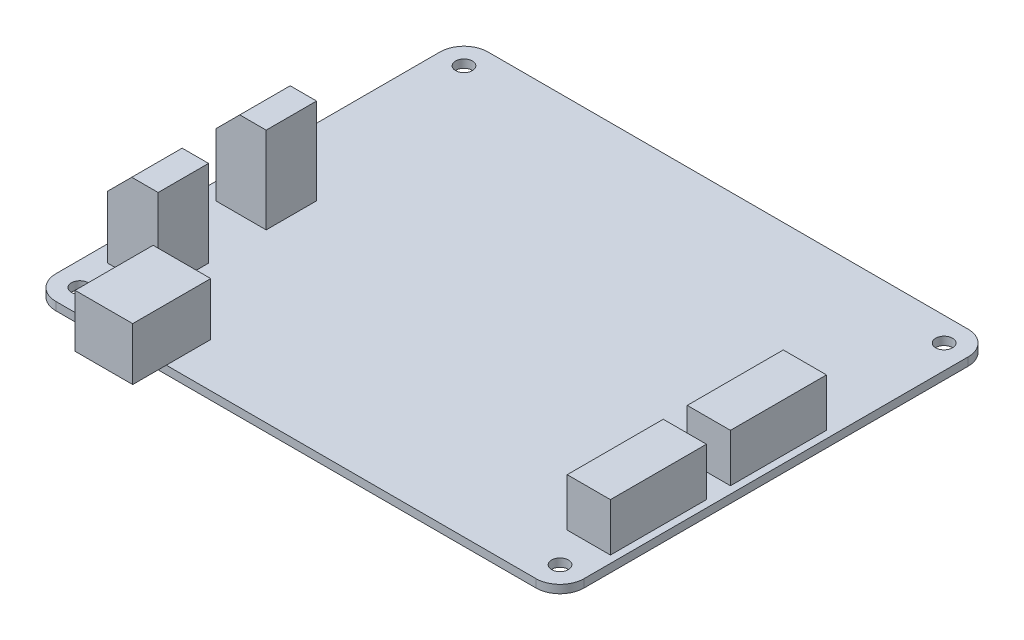
SolidWorks part; units mm, degrees
ref_plane "Front Plane" through (0, 0, 0) normal (0, 0, 1) x (1, 0, 0)
ref_plane "Top Plane" through (0, 0, 0) normal (0, 1, 0) x (1, 0, 0)
ref_plane "Right Plane" through (0, 0, 0) normal (1, 0, 0) x (0, 0, -1)
sketch "Sketch1" plane through (0, 0, 0) normal (0, 1, 0) x (1, 0, 0)
  line L1 (-55, -45) -> (55, -45)
  line L2 (-55, -45) -> (-55, 45)
  line L3 (-55, 45) -> (55, 45)
  line L4 (55, -45) -> (55, 45)
  line L5 (-55, -45) -> (55, 45) construction
  line L6 (-55, 45) -> (55, -45) construction
  point P0 (0, 0)
  dimension "D1" = 110
  dimension "D2" = 90
extrude "Boss-Extrude1" add sketch "Sketch1" along normal blind 1.7
sketch "Sketch2" plane through (0, 1.7, 0) normal (0, 1, 0) x (1, 0, 0)
  line L0 (0, 45) -> (0, -45) construction
  line L1 (55, 45) -> (-55, 45) construction
  line L2 (-55, -45) -> (55, -45) construction
  line L3 (-55, 0) -> (55, 0) construction
  line L4 (-55, 45) -> (-55, -45) construction
  line L5 (55, -45) -> (55, 45) construction
  circle A0 centre (-50, 40) radius 1.75
  circle A1 centre (-50, -40) radius 1.75
  circle A2 centre (50, -40) radius 1.75
  circle A3 centre (50, 40) radius 1.75
  dimension "D1" = 3.5
  dimension "D2" = 40
  dimension "D3" = 50
extrude "Cut-Extrude1" cut sketch "Sketch2" against normal up to next and the other way through all
fillet "Fillet1" radius 5 4 edges at (55, 0.85, -45) (55, 0.85, 45) (-55, 0.85, 45) (-55, 0.85, -45)
sketch "Sketch3" plane through (0, 1.7, 0) normal (0, 1, 0) x (1, 0, 0)
  line L0 (-50, -45) -> (50, -45) construction
  line L1 (-51.5, -32.7) -> (-41, -32.7)
  line L2 (-51.5, -32.7) -> (-51.5, -22.2)
  line L3 (-51.5, -22.2) -> (-41, -22.2)
  line L4 (-41, -32.7) -> (-41, -22.2)
  line L5 (-55, 40) -> (-55, -40) construction
  line L6 (-51.5, -10.2) -> (-51.5, 0.3)
  line L7 (-51.5, -10.2) -> (-41, -10.2)
  line L8 (-41, -10.2) -> (-41, 0.3)
  line L9 (-51.5, 0.3) -> (-41, 0.3)
  dimension "D1" = 10.5
  dimension "D2" = 12.3
  dimension "D3" = 10.5
  dimension "D4" = 3.5
  dimension "D6" = 12
  dimension "D5" = 2
extrude "Boss-Extrude2" add sketch "Sketch3" along normal blind 18
chamfer "Chamfer1" distance 5 angle 45 2 edges at (-51.5, 19.7, 27.45) (-51.5, 19.7, 4.95)
sketch "Sketch4" plane through (0, 1.7, 0) normal (0, 1, 0) x (1, 0, 0)
  line L0 (-50, -45) -> (50, -45) construction
  line L1 (-39, -35.75) -> (-27, -35.75)
  line L2 (-39, -35.75) -> (-39, -52)
  line L3 (-39, -52) -> (-27, -52)
  line L4 (-27, -35.75) -> (-27, -52)
  line L5 (-55, 40) -> (-55, -40) construction
  dimension "D1" = 16.25
  dimension "D2" = 7
  dimension "D3" = 12
  dimension "D4" = 16
extrude "Boss-Extrude3" add sketch "Sketch4" along normal blind 11
sketch "Sketch5" plane through (0, 1.7, 0) normal (0, 1, 0) x (1, 0, 0)
  line L0 (-27, -45) -> (50, -45) construction
  line L1 (44.5, -33) -> (53.5, -33)
  line L2 (44.5, -33) -> (44.5, -13)
  line L3 (44.5, -13) -> (53.5, -13)
  line L4 (53.5, -33) -> (53.5, -13)
  line L5 (55, -40) -> (55, 40) construction
  line L6 (44.5, -8) -> (44.5, 12)
  line L7 (44.5, -8) -> (53.5, -8)
  line L8 (53.5, -8) -> (53.5, 12)
  line L9 (44.5, 12) -> (53.5, 12)
  dimension "D1" = 20
  dimension "D2" = 12
  dimension "D3" = 9
  dimension "D4" = 1.5
  dimension "D6" = 5
  dimension "D5" = 2
extrude "Boss-Extrude4" add sketch "Sketch5" along normal blind 10
